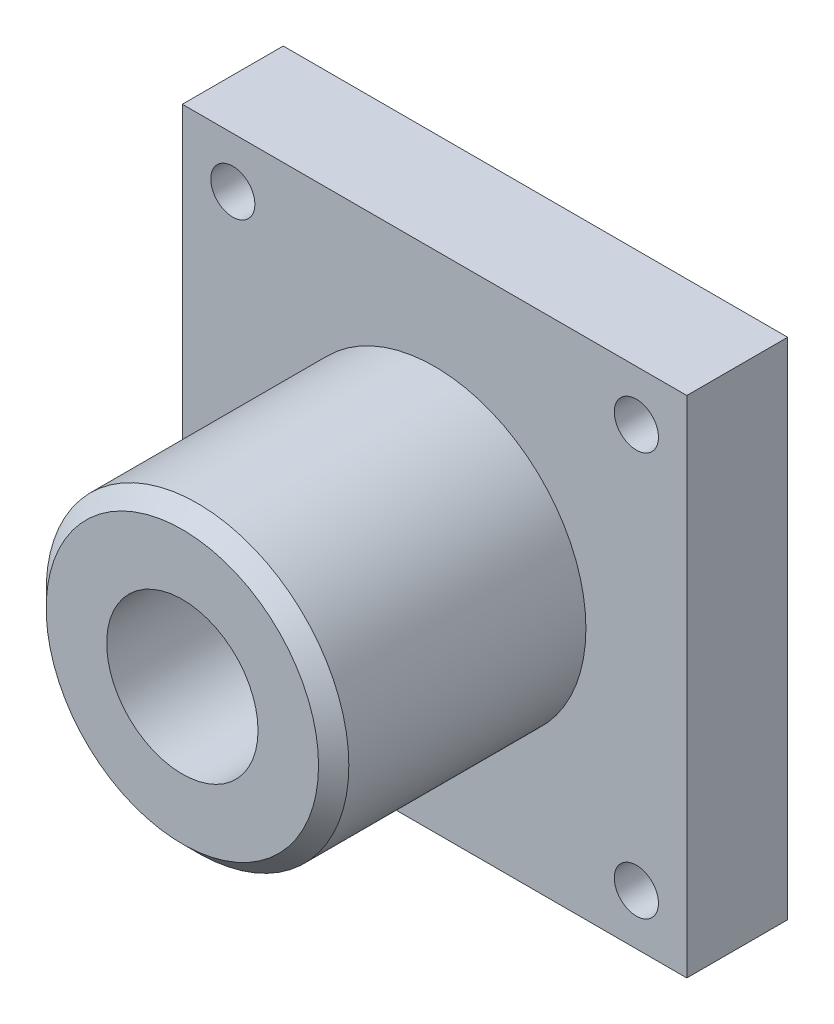
SolidWorks part; units mm, degrees
material "Gray Cast Iron"
ref_plane "Front Plane" through (0, 0, 0) normal (0, 0, 1) x (1, 0, 0)
ref_plane "Top Plane" through (0, 0, 0) normal (0, 1, 0) x (1, 0, 0)
ref_plane "Right Plane" through (0, 0, 0) normal (1, 0, 0) x (0, 0, -1)
sketch "Sketch1" plane through (0, 0, 0) normal (0, 0, 1) x (1, 0, 0)
  line L1 (-127, 127) -> (127, 127)
  line L2 (-127, 127) -> (-127, -127)
  line L3 (-127, -127) -> (127, -127)
  line L4 (127, 127) -> (127, -127)
  line L5 (-127, 127) -> (127, -127) construction
  line L6 (-127, -127) -> (127, 127) construction
  point P0 (0, 0)
  dimension "D1" = 254
  dimension "D2" = 254
extrude "Boss-Extrude1" add sketch "Sketch1" along normal blind 50.8
sketch "Sketch2" plane through (0, 0, 50.8) normal (0, 0, 1) x (1, 0, 0)
  circle A0 centre (0, 0) radius 76.2
  dimension "D1" = 152.4
extrude "Boss-Extrude2" add sketch "Sketch2" along normal blind 127
chamfer "Chamfer1" distance 7.62 angle 45 1 edges at (76.2, 0, 177.8)
sketch "Sketch3" plane through (0, 0, 177.8) normal (0, 0, 1) x (1, 0, 0)
  circle A0 centre (0, 0) radius 38.1
  dimension "D1" = 76.2
extrude "Cut-Extrude1" cut sketch "Sketch3" against normal through all
hole_wizard "7/8 (0.875) Diameter Hole1" positions "Sketch5" profile "Sketch4" hole size "7/8" standard "Ansi Inch" end condition through all
sketch "Sketch5" plane through (0, 0, 50.8) normal (0, 0, 1) x (1, 0, 0)
  line L0 (127, -127) -> (127, 127) construction
  line L1 (127, 127) -> (-127, 127) construction
  line L2 (-127, 127) -> (-127, -127) construction
  line L3 (-127, -127) -> (127, -127) construction
  point P0 (-101.6, 101.6)
  point P1 (101.6, 101.6)
  point P3 (101.6, -101.6)
  point P5 (-101.6, -101.6)
  dimension "D1" = 25.4
  dimension "D2" = 25.4
  dimension "D3" = 25.4
  dimension "D4" = 25.4
sketch "Sketch4" plane through (-101.6, 101.6, 50.8) normal (1, 0, 0) x (0, -1, 0)
  line L0 (0, 0) -> (0, 50.8)
  line L1 (0, 50.8) -> (11.1125, 50.8)
  line L2 (11.1125, 50.8) -> (11.1125, 0)
  line L5 (11.1125, 0) -> (0, 0)
  line L11 (0, -6.35) -> (0, 107.95) construction
  dimension "Thru Hole Dia." = 22.225
  dimension "Thru Hole Depth" = 50.8
